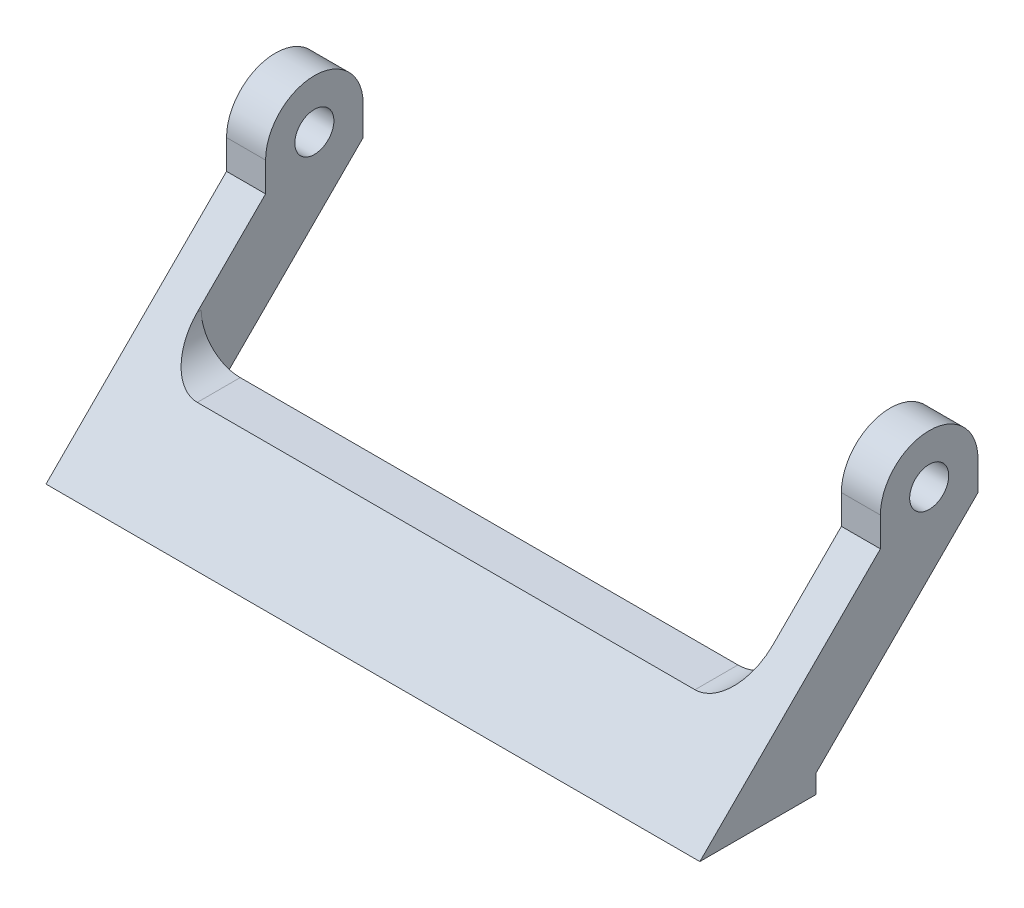
SolidWorks part; units mm, degrees
ref_plane "Front Plane" through (0, 0, 0) normal (0, 0, 1) x (1, 0, 0)
ref_plane "Top Plane" through (0, 0, 0) normal (0, 1, 0) x (1, 0, 0)
ref_plane "Right Plane" through (0, 0, 0) normal (1, 0, 0) x (0, 0, -1)
sketch "Sketch1" plane through (0, 0, 0) normal (1, 0, 0) x (0, 0, -1)
  line L0 (11.9, 1.9) -> (11.9, 0)
  line L1 (11.9, 0) -> (0, 0)
  line L2 (0, 0) -> (18.5, 18.5)
  line L3 (18.5, 18.5) -> (18.5, 21.5)
  line L4 (28.5, 21.5) -> (28.5, 18.5)
  line L5 (28.5, 18.5) -> (11.9, 1.9)
  arc A0 (18.5, 21.5) -> (28.5, 21.5) centre (23.5, 21.5) cw
  circle A1 centre (23.5, 21.5) radius 2
  dimension "D6" = 4
  dimension "D1" = 11.9
  dimension "D2" = 45
  dimension "D3" = 10
  dimension "D4" = 1.9
  dimension "D5" = 18.5
  dimension "D7" = 21.5
extrude "Boss-Extrude1" add sketch "Sketch1" along normal blind 67
sketch "Sketch2" plane through (0, 0, -28.5) normal (0, 0, -1) x (-1, 0, 0)
  line L0 (-63, 26.5) -> (-63, 11.5)
  line L1 (0, 26.5) -> (-67, 26.5) construction
  line L2 (-59, 7.5) -> (-8, 7.5)
  line L3 (-4, 11.5) -> (-4, 26.5)
  line L4 (-4, 26.5) -> (-63, 26.5)
  line L5 (-67, 1.9) -> (-67, 18.5) construction
  line L6 (0, 21.5) -> (0, 26.5) construction
  line L7 (-67, 0) -> (0, 0) construction
  arc A0 (-8, 7.5) -> (-4, 11.5) centre (-8, 11.5) ccw
  arc A1 (-63, 11.5) -> (-59, 7.5) centre (-59, 11.5) ccw
  dimension "D4" = 4
  dimension "D1" = 4
  dimension "D2" = 4
  dimension "D3" = 7.5
extrude "Cut-Extrude1" cut sketch "Sketch2" against normal up to next
sketch "Sketch3" plane through (0, 0, 0) normal (0, -1, 0) x (1, 0, 0)
  line L0 (4, -21.5) -> (63, -21.5)
  line L1 (4, -21.5) -> (4, -11.9)
  line L2 (63, -21.5) -> (63, -11.9)
  line L3 (4, -11.9) -> (63, -11.9)
  line L4 (67, -11.9) -> (0, -11.9) construction
extrude "Cut-Extrude2" cut sketch "Sketch3" against normal up to next
